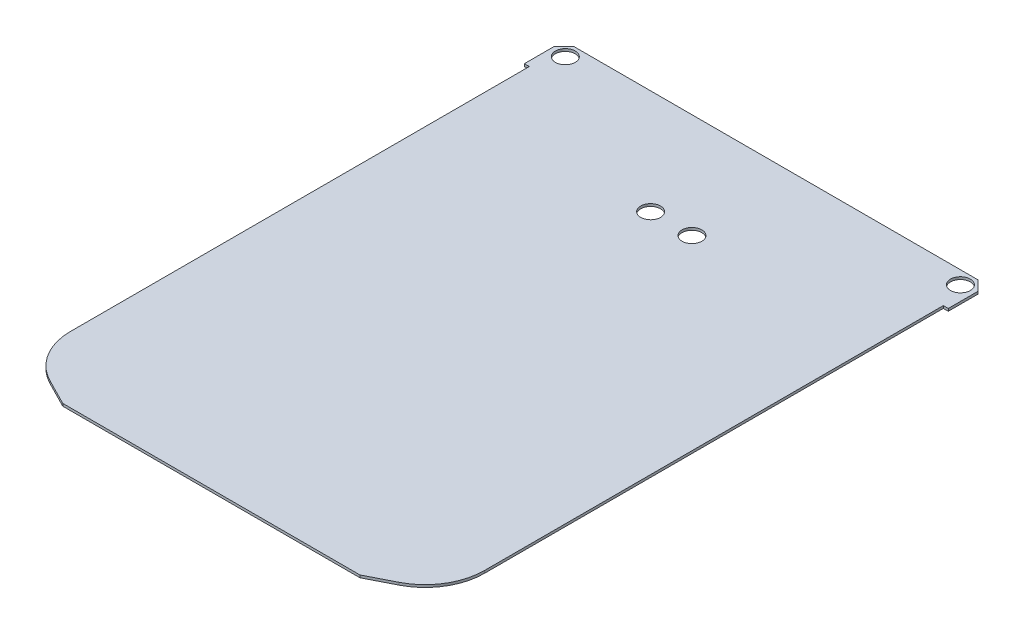
SolidWorks part; units mm, degrees
ref_plane "Front Plane" through (0, 0, 0) normal (0, 0, 1) x (1, 0, 0)
ref_plane "Top Plane" through (0, 0, 0) normal (0, 1, 0) x (1, 0, 0)
ref_plane "Right Plane" through (0, 0, 0) normal (1, 0, 0) x (0, 0, -1)
sketch "Sketch1" plane through (0, 0, 0) normal (0, 1, 0) x (1, 0, 0)
  line L0 (-21.4, 26.5) -> (-20.9, 26.5)
  line L3 (-21.4, 29.5) -> (-21.4, 26.5)
  line L11 (-20.4, 30.5) -> (20.4, 30.5)
  line L17 (0, 30.5) -> (0, -30.5) construction
  line L21 (21.4, 29.5) -> (21.4, 26.5)
  line L22 (21.4, 26.5) -> (20.9, 26.5)
  line L23 (-20.9, 26.5) -> (-20.9, -23.5)
  line L24 (-20.9, -23.5) -> (20.9, -23.5) construction
  line L25 (20.9, -23.5) -> (20.9, 26.5)
  line L26 (-15, -26.5) -> (15, -26.5)
  line L29 (-20.9, -23.5) -> (-15, -26.5)
  line L30 (15, -26.5) -> (20.9, -23.5)
  line L31 (-21.4, 29.5) -> (-20.4, 30.5)
  line L32 (21.4, 29.5) -> (20.4, 30.5)
  circle A6 centre (-19.9444, 29.1814) radius 1
  circle A8 centre (19.9444, 29.1814) radius 1
  point P17 (0, 0)
  point P19 (0, -26.5)
  dimension "D6" = 30.5
  dimension "D9" = 40.8
  dimension "D3" = 29.1814
  dimension "D5" = 45
  dimension "D2" = 19.9444
  dimension "D12" = 2
  dimension "D4" = 50
  dimension "D7" = 35.9
  dimension "D8" = 3
  dimension "D10" = 26.5
  dimension "D11" = 20.9
  dimension "D13" = 0.5
extrude "Boss-Extrude1" add sketch "Sketch1" along normal blind 0.25
sketch "Sketch2" plane through (0, 0.25, 0) normal (0, 1, 0) x (1, 0, 0)
  circle A0 centre (-2.0845, 19.9345) radius 1
  circle A1 centre (2.0845, 19.9345) radius 1
extrude "Cut-Extrude1" cut sketch "Sketch2" against normal blind 4.5
sketch "Sketch3" plane through (0, 0.25, 0) normal (0, 1, 0) x (1, 0, 0)
  line L1 (-9.09, -23.1) -> (-8.69, -23.1) construction
  line L2 (-9.09, -21.43) -> (9.09, -21.43) construction
  line L3 (-9.09, -21.43) -> (-9.09, -23.1) construction
  line L4 (-9.09, -23.1) -> (9.09, -23.1) construction
  line L5 (9.09, -21.43) -> (9.09, -23.1) construction
  line L6 (-9.09, -21.43) -> (9.09, -23.1) construction
  line L7 (-9.09, -23.1) -> (9.09, -21.43) construction
  line L8 (-9.09, -22.13) -> (-9.09, -24.2) construction
  line L9 (9.09, -22.13) -> (9.09, -21.43) construction
  point P6 (0, -22.265)
fillet "Fillet1" radius 6 2 edges at (20.9, 0.125, 23.5) (-20.9, 0.125, 23.5)
